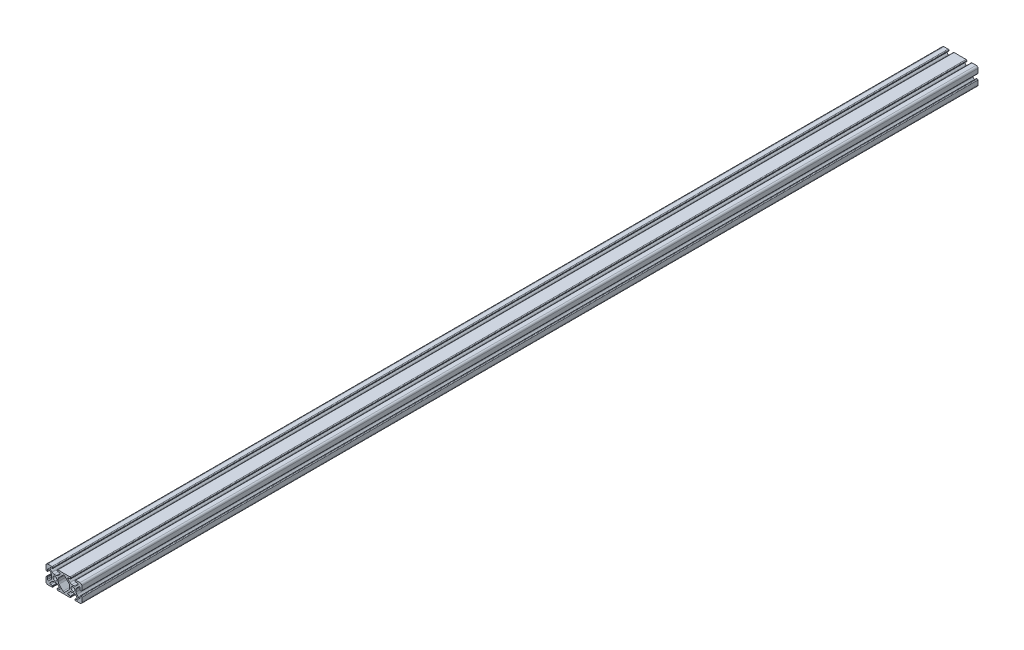
SolidWorks part; units mm, degrees
material "6061 Alloy"
ref_plane "Front Plane" through (0, 0, 0) normal (0, 0, 1) x (1, 0, 0)
ref_plane "Top Plane" through (0, 0, 0) normal (0, 1, 0) x (1, 0, 0)
ref_plane "Right Plane" through (0, 0, 0) normal (1, 0, 0) x (0, 0, -1)
sketch "Sketch1" plane through (0, 0, 0) normal (0, 0, 1) x (1, 0, 0)
  line L2 (-19.9898, 7.9883) -> (-19.9898, 3.2893)
  line L3 (-17.9832, 9.9949) -> (-13.2842, 9.9949)
  line L4 (-12.4968, 9.2075) -> (-12.4968, 8.4963)
  line L5 (-12.8016, 8.1915) -> (-14.9098, 8.1915)
  line L6 (-15.5025, 6.7606) -> (-13.2477, 4.5058)
  line L7 (-16.7555, 5.5076) -> (-14.5007, 3.2528)
  line L8 (-18.1864, 4.9149) -> (-18.1864, 2.8067)
  line L9 (-18.4912, 2.5019) -> (-19.2024, 2.5019)
  line L11 (-11.1283, 3.6279) -> (-8.8615, 3.6279)
  line L12 (-13.6228, 1.1334) -> (-13.6228, -1.1334)
  line L13 (0, 9.9949) -> (-6.7056, 9.9949)
  line L14 (-7.493, 9.2075) -> (-7.493, 8.4963)
  line L15 (-7.1882, 8.1915) -> (-5.08, 8.1915)
  line L16 (-6.367, 1.1334) -> (-6.367, -1.1334)
  line L17 (-4.4873, 6.7606) -> (-6.7421, 4.5058)
  line L18 (-0.9396, 7.8023) -> (-5.4891, 3.2528)
  line L19 (-18.4912, -2.5019) -> (-19.2024, -2.5019)
  line L20 (-18.1864, -4.9149) -> (-18.1864, -2.8067)
  line L21 (-16.7555, -5.5076) -> (-14.5007, -3.2528)
  line L22 (-15.5025, -6.7606) -> (-13.2477, -4.5058)
  line L23 (-12.8016, -8.1915) -> (-14.9098, -8.1915)
  line L24 (-12.4968, -9.2075) -> (-12.4968, -8.4963)
  line L25 (-17.9832, -9.9949) -> (-13.2842, -9.9949)
  line L26 (-19.9898, -7.9883) -> (-19.9898, -3.2893)
  line L27 (0, -9.9949) -> (-6.7056, -9.9949)
  line L28 (-7.493, -9.2075) -> (-7.493, -8.4963)
  line L29 (-7.1882, -8.1915) -> (-5.08, -8.1915)
  line L30 (-4.4873, -6.7606) -> (-6.7421, -4.5058)
  line L31 (-0.9396, -7.8023) -> (-5.4891, -3.2528)
  line L32 (-11.1283, -3.6279) -> (-8.8615, -3.6279)
  line L34 (11.1283, -3.6279) -> (8.8615, -3.6279)
  line L35 (0.9396, -7.8023) -> (5.4891, -3.2528)
  line L36 (4.4873, -6.7606) -> (6.7421, -4.5058)
  line L37 (7.1882, -8.1915) -> (5.08, -8.1915)
  line L38 (7.493, -9.2075) -> (7.493, -8.4963)
  line L39 (0, -9.9949) -> (6.7056, -9.9949)
  line L40 (19.9898, -7.9883) -> (19.9898, -3.2893)
  line L41 (17.9832, -9.9949) -> (13.2842, -9.9949)
  line L42 (12.4968, -9.2075) -> (12.4968, -8.4963)
  line L43 (12.8016, -8.1915) -> (14.9098, -8.1915)
  line L44 (15.5025, -6.7606) -> (13.2477, -4.5058)
  line L45 (16.7555, -5.5076) -> (14.5007, -3.2528)
  line L46 (18.1864, -4.9149) -> (18.1864, -2.8067)
  line L47 (18.4912, -2.5019) -> (19.2024, -2.5019)
  line L48 (0.9396, 7.8023) -> (5.4891, 3.2528)
  line L49 (4.4873, 6.7606) -> (6.7421, 4.5058)
  line L50 (6.367, 1.1334) -> (6.367, -1.1334)
  line L51 (7.1882, 8.1915) -> (5.08, 8.1915)
  line L52 (7.493, 9.2075) -> (7.493, 8.4963)
  line L53 (0, 9.9949) -> (6.7056, 9.9949)
  line L54 (13.6228, 1.1334) -> (13.6228, -1.1334)
  line L55 (11.1283, 3.6279) -> (8.8615, 3.6279)
  line L56 (18.4912, 2.5019) -> (19.2024, 2.5019)
  line L57 (18.1864, 4.9149) -> (18.1864, 2.8067)
  line L58 (16.7555, 5.5076) -> (14.5007, 3.2528)
  line L59 (15.5025, 6.7606) -> (13.2477, 4.5058)
  line L60 (12.8016, 8.1915) -> (14.9098, 8.1915)
  line L61 (12.4968, 9.2075) -> (12.4968, 8.4963)
  line L62 (17.9832, 9.9949) -> (13.2842, 9.9949)
  line L63 (19.9898, 7.9883) -> (19.9898, 3.2893)
  circle A0 centre (-9.9949, 0) radius 2.1463
  arc A1 (-19.9898, 7.9883) -> (-17.9832, 9.9949) centre (-17.9832, 7.9883) cw
  arc A2 (-16.7555, 5.5076) -> (-18.1864, 4.9149) centre (-17.3482, 4.9149) ccw
  arc A3 (-14.9098, 8.1915) -> (-15.5025, 6.7606) centre (-14.9098, 7.3533) ccw
  arc A4 (-13.2842, 9.9949) -> (-12.4968, 9.2075) centre (-13.2842, 9.2075) cw
  arc A5 (-19.9898, 3.2893) -> (-19.2024, 2.5019) centre (-19.2024, 3.2893) ccw
  arc A6 (-18.1864, 2.8067) -> (-18.4912, 2.5019) centre (-18.4912, 2.8067) cw
  arc A7 (-12.4968, 8.4963) -> (-12.8016, 8.1915) centre (-12.8016, 8.4963) cw
  arc A8 (-11.1283, 3.6279) -> (-13.2477, 4.5058) centre (-11.1283, 6.6251) cw
  arc A9 (-13.6228, 1.1334) -> (-14.5007, 3.2528) centre (-16.62, 1.1334) ccw
  arc A10 (0.9396, 7.8023) -> (-0.9396, 7.8023) centre (0, 6.8627) ccw
  arc A11 (-0.9396, -7.8023) -> (0.9396, -7.8023) centre (0, -6.8627) ccw
  arc A12 (-6.7056, 9.9949) -> (-7.493, 9.2075) centre (-6.7056, 9.2075) ccw
  arc A13 (-7.493, 8.4963) -> (-7.1882, 8.1915) centre (-7.1882, 8.4963) ccw
  arc A14 (-8.8615, 3.6279) -> (-6.7421, 4.5058) centre (-8.8615, 6.6251) ccw
  arc A15 (-6.367, 1.1334) -> (-5.4891, 3.2528) centre (-3.3698, 1.1334) cw
  arc A16 (-5.08, 8.1915) -> (-4.4873, 6.7606) centre (-5.08, 7.3533) cw
  arc A17 (-13.6228, -1.1334) -> (-14.5007, -3.2528) centre (-16.62, -1.1334) cw
  arc A18 (-11.1283, -3.6279) -> (-13.2477, -4.5058) centre (-11.1283, -6.6251) ccw
  arc A19 (-12.4968, -8.4963) -> (-12.8016, -8.1915) centre (-12.8016, -8.4963) ccw
  arc A20 (-18.1864, -2.8067) -> (-18.4912, -2.5019) centre (-18.4912, -2.8067) ccw
  arc A21 (-19.9898, -3.2893) -> (-19.2024, -2.5019) centre (-19.2024, -3.2893) cw
  arc A22 (-13.2842, -9.9949) -> (-12.4968, -9.2075) centre (-13.2842, -9.2075) ccw
  arc A23 (-14.9098, -8.1915) -> (-15.5025, -6.7606) centre (-14.9098, -7.3533) cw
  arc A24 (-16.7555, -5.5076) -> (-18.1864, -4.9149) centre (-17.3482, -4.9149) cw
  arc A25 (-19.9898, -7.9883) -> (-17.9832, -9.9949) centre (-17.9832, -7.9883) ccw
  arc A26 (-5.08, -8.1915) -> (-4.4873, -6.7606) centre (-5.08, -7.3533) ccw
  arc A27 (-6.7056, -9.9949) -> (-7.493, -9.2075) centre (-6.7056, -9.2075) cw
  arc A28 (-7.493, -8.4963) -> (-7.1882, -8.1915) centre (-7.1882, -8.4963) cw
  arc A29 (-8.8615, -3.6279) -> (-6.7421, -4.5058) centre (-8.8615, -6.6251) cw
  arc A30 (-6.367, -1.1334) -> (-5.4891, -3.2528) centre (-3.3698, -1.1334) ccw
  arc A31 (6.367, -1.1334) -> (5.4891, -3.2528) centre (3.3698, -1.1334) cw
  arc A32 (8.8615, -3.6279) -> (6.7421, -4.5058) centre (8.8615, -6.6251) ccw
  arc A33 (7.493, -8.4963) -> (7.1882, -8.1915) centre (7.1882, -8.4963) ccw
  arc A34 (6.7056, -9.9949) -> (7.493, -9.2075) centre (6.7056, -9.2075) ccw
  arc A35 (5.08, -8.1915) -> (4.4873, -6.7606) centre (5.08, -7.3533) cw
  arc A36 (19.9898, -7.9883) -> (17.9832, -9.9949) centre (17.9832, -7.9883) cw
  arc A37 (16.7555, -5.5076) -> (18.1864, -4.9149) centre (17.3482, -4.9149) ccw
  arc A38 (14.9098, -8.1915) -> (15.5025, -6.7606) centre (14.9098, -7.3533) ccw
  arc A39 (13.2842, -9.9949) -> (12.4968, -9.2075) centre (13.2842, -9.2075) cw
  arc A40 (19.9898, -3.2893) -> (19.2024, -2.5019) centre (19.2024, -3.2893) ccw
  arc A41 (18.1864, -2.8067) -> (18.4912, -2.5019) centre (18.4912, -2.8067) cw
  arc A42 (12.4968, -8.4963) -> (12.8016, -8.1915) centre (12.8016, -8.4963) cw
  arc A43 (11.1283, -3.6279) -> (13.2477, -4.5058) centre (11.1283, -6.6251) cw
  arc A44 (13.6228, -1.1334) -> (14.5007, -3.2528) centre (16.62, -1.1334) ccw
  arc A45 (5.08, 8.1915) -> (4.4873, 6.7606) centre (5.08, 7.3533) ccw
  arc A46 (6.367, 1.1334) -> (5.4891, 3.2528) centre (3.3698, 1.1334) ccw
  arc A47 (8.8615, 3.6279) -> (6.7421, 4.5058) centre (8.8615, 6.6251) cw
  arc A48 (7.493, 8.4963) -> (7.1882, 8.1915) centre (7.1882, 8.4963) cw
  arc A49 (6.7056, 9.9949) -> (7.493, 9.2075) centre (6.7056, 9.2075) cw
  arc A50 (13.6228, 1.1334) -> (14.5007, 3.2528) centre (16.62, 1.1334) cw
  arc A51 (11.1283, 3.6279) -> (13.2477, 4.5058) centre (11.1283, 6.6251) ccw
  arc A52 (12.4968, 8.4963) -> (12.8016, 8.1915) centre (12.8016, 8.4963) ccw
  arc A53 (18.1864, 2.8067) -> (18.4912, 2.5019) centre (18.4912, 2.8067) ccw
  arc A54 (19.9898, 3.2893) -> (19.2024, 2.5019) centre (19.2024, 3.2893) cw
  arc A55 (13.2842, 9.9949) -> (12.4968, 9.2075) centre (13.2842, 9.2075) ccw
  arc A56 (14.9098, 8.1915) -> (15.5025, 6.7606) centre (14.9098, 7.3533) cw
  arc A57 (16.7555, 5.5076) -> (18.1864, 4.9149) centre (17.3482, 4.9149) cw
  arc A58 (19.9898, 7.9883) -> (17.9832, 9.9949) centre (17.9832, 7.9883) ccw
  circle A59 centre (9.9949, 0) radius 2.1463
  point P186 (9.9949, 3.6279)
extrude "Boss-Extrude1" add sketch "Sketch1" along normal mid plane 1000
ref_plane "Plane1" through (-9.9949, 0, 0) normal (-1, 0, 0) x (0, 0, 1)
